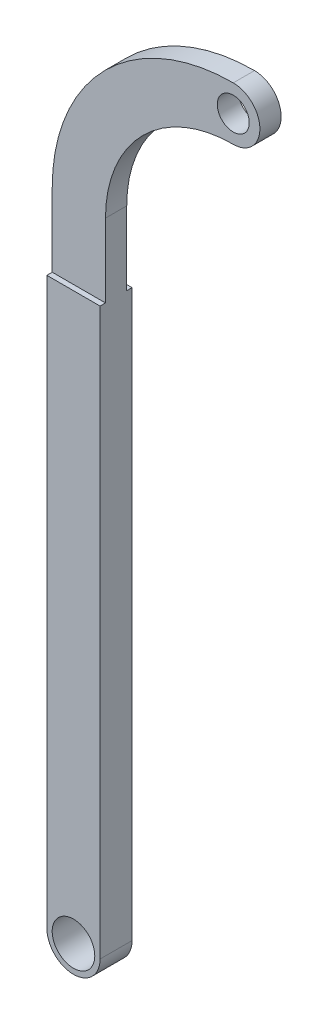
SolidWorks part; units mm, degrees
material "7075-O (SS)"
ref_plane "前视基准面" through (0, 0, 0) normal (0, 0, 1) x (1, 0, 0)
ref_plane "上视基准面" through (0, 0, 0) normal (0, 1, 0) x (1, 0, 0)
ref_plane "右视基准面" through (0, 0, 0) normal (1, 0, 0) x (0, 0, -1)
sketch "草图1" plane through (0, 0, 0) normal (0, 0, 1) x (1, 0, 0)
  line L0 (-2.5, 0) -> (-2.5, 60)
  line L1 (2.5, 0) -> (2.5, 60)
  line L3 (14.5, 77) -> (14.5, 72) construction
  circle A0 centre (0, 0) radius 2
  arc A1 (-2.5, 0) -> (2.5, 0) centre (0, 0) ccw
  arc A2 (14.5, 72) -> (2.5, 60) centre (14.5, 60) ccw
  arc A3 (14.5, 77) -> (-2.5, 60) centre (14.5, 60) ccw
  arc A4 (14.5, 72) -> (14.5, 77) centre (14.5, 74.5) ccw
  circle A5 centre (14.5, 74.5) radius 1.5
  dimension "D1" = 4
  dimension "D2" = 3
  dimension "D3" = 2.5
extrude "凸台-拉伸1" add sketch "草图1" along normal blind 3
sketch "草图2" plane through (0, 0, 0) normal (1, 0, 0) x (0, 0, -1)
  line L0 (-0.5, 77) -> (0, 77)
  line L1 (-3, 77) -> (0, 77) construction
  line L2 (-0.5, 77) -> (-0.5, 53.1001)
  line L3 (-0.5, 53.1001) -> (0, 53.1001)
  line L4 (0, 0) -> (0, 60) construction
  line L5 (0, 53.1001) -> (0, 77)
  line L6 (-3.0848, 77) -> (-2.4953, 77)
  line L7 (-3.0848, 77) -> (-3.0848, 53.1001)
  line L8 (-3.0848, 53.1001) -> (-2.4953, 53.1001)
  line L9 (-2.4953, 53.1001) -> (-2.4953, 77)
extrude "切除-拉伸1" cut sketch "草图2" against normal through all and the other way through all
